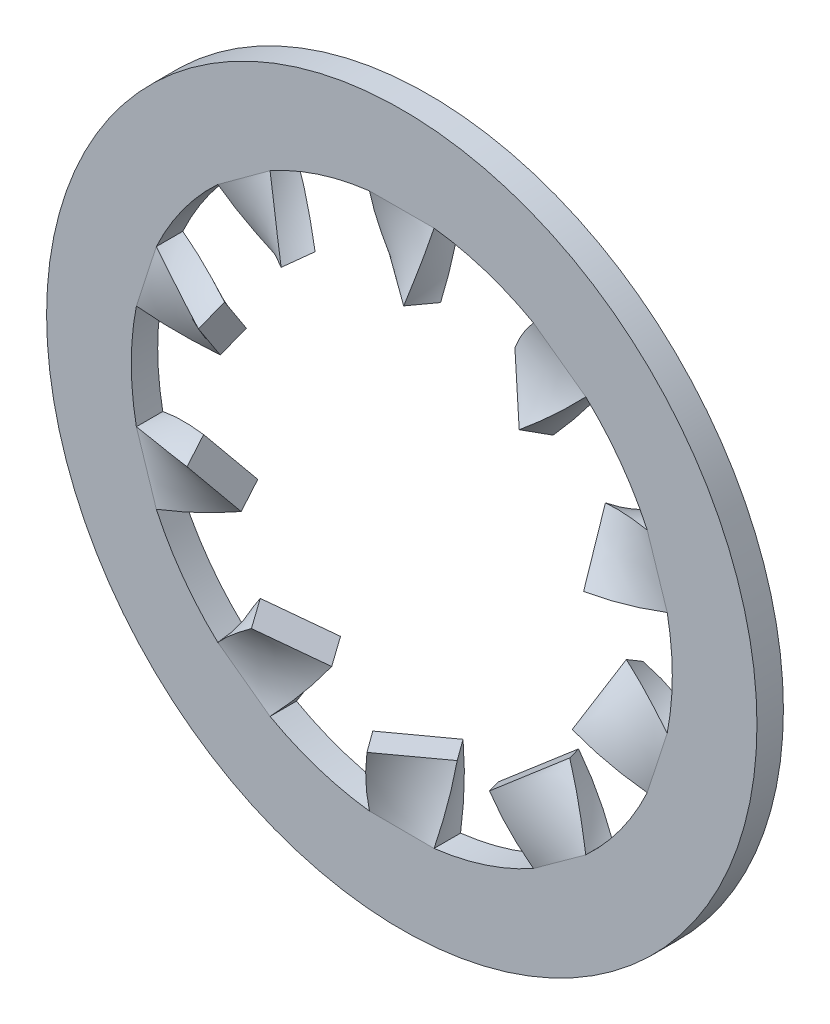
SolidWorks part; units mm, degrees
ref_plane "Спереди" through (0, 0, 0) normal (0, 0, 1) x (1, 0, 0)
ref_plane "Сверху" through (0, 0, 0) normal (0, 1, 0) x (1, 0, 0)
ref_plane "Справа" through (0, 0, 0) normal (1, 0, 0) x (0, 0, -1)
sketch "Эскиз1" plane through (0, 0, 0) normal (0, 0, 1) x (1, 0, 0)
  line L0 (-0.9777, 6.1731) -> (0, 0) construction
  line L1 (-0.9777, 8.1285) -> (0.9777, 8.1285)
  line L2 (-0.9777, 8.1285) -> (-0.9777, 6.1731)
  line L3 (-0.9777, 6.1731) -> (0.9777, 6.1731)
  line L4 (0.9777, 8.1285) -> (0.9777, 6.1731)
  line L5 (0, 0) -> (0.9777, 6.1731) construction
  line L6 (0, 6.1731) -> (0, 0) construction
  line L7 (3.9868, 7.1508) -> (5.5688, 6.0014)
  line L8 (7.4285, 3.4417) -> (8.0328, 1.582)
  line L9 (8.0328, -1.582) -> (7.4285, -3.4417)
  line L10 (5.5688, -6.0014) -> (3.9868, -7.1508)
  line L11 (0.9777, -8.1285) -> (-0.9777, -8.1285)
  line L12 (-3.9868, -7.1508) -> (-5.5688, -6.0014)
  line L13 (-7.4285, -3.4417) -> (-8.0328, -1.582)
  line L14 (-8.0328, 1.582) -> (-7.4285, 3.4417)
  line L15 (-5.5688, 6.0014) -> (-3.9868, 7.1508)
  circle A0 centre (0, 0) radius 6.25
  circle A1 centre (0, 0) radius 10.75
  circle A2 centre (0, 0) radius 8.1871
  point P31 (0, 0)
  dimension "D1" = 12.5
  dimension "D2" = 21.5
  dimension "D3" = 18
  dimension "D4" = 10
extrude "Бобышка-Вытянуть1" add sketch "Эскиз1" along normal blind 0.8 contours A1 A2 | L1 A2 | L7 A2 | L8 A2 | L9 A2 | L10 A2 | L11 A2 | L12 A2 | L13 A2 | L14 A2 | L15 A2
sketch "Эскиз2" plane through (0, 8.1285, 0) normal (0, -1, 0) x (1, 0, 0)
  line L0 (-0.9777, 0) -> (0.9777, 0.8) construction
  circle A0 centre (0, 0.4) radius 1.0564
curve "Спираль1" pitch 20 height 2 turns 0.1
sketch "Эскиз3" plane through (0, 8.1285, 0) normal (0, -1, 0) x (1, 0, 0)
  line L8 (-0.9777, 0) -> (0.9777, 0)
  line L9 (0.9777, 0) -> (0.9777, 0.8)
  line L10 (0.9777, 0.8) -> (-0.9777, 0.8)
  line L11 (-0.9777, 0.8) -> (-0.9777, 0)
  line L12 (-0.9777, 0) -> (0.9777, 0)
  line L13 (0.9777, 0) -> (0.9777, 0.8)
  line L14 (0.9777, 0.8) -> (-0.9777, 0.8)
  line L15 (-0.9777, 0.8) -> (-0.9777, 0)
  dimension "D1" = 0
sweep "По траектории1" add profiles "Эскиз3" path "Спираль1"
sketch "Эскиз4" plane through (0, 0, 0) normal (1, 0, 0) x (0, 0, -1)
  line L0 (0, 0) -> (7.4536, 0) construction
  line L1 (0, -10.75) -> (0, 10.75) construction
pattern_circular "Круговой массив1" count 10 every 36 about axis through (0, 0, 0) along (0, 0, -1) of "По траектории1"
